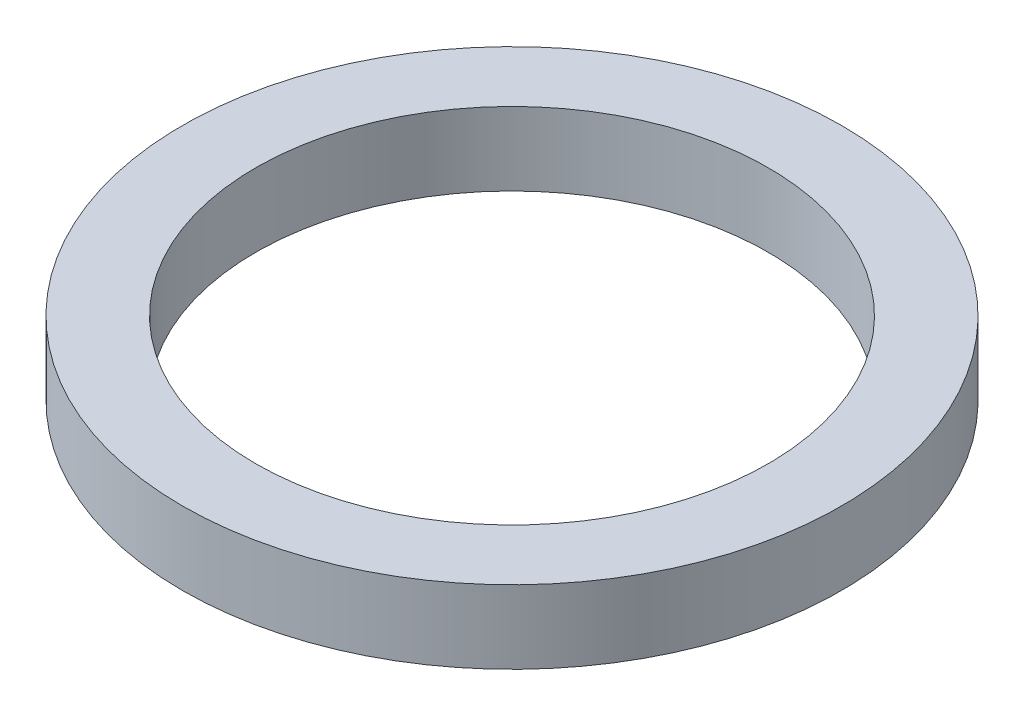
SolidWorks part; units mm, degrees
material "1060 Alloy"
ref_plane "Front Plane" through (0, 0, 0) normal (0, 0, 1) x (1, 0, 0)
ref_plane "Top Plane" through (0, 0, 0) normal (0, 1, 0) x (1, 0, 0)
ref_plane "Right Plane" through (0, 0, 0) normal (1, 0, 0) x (0, 0, -1)
sketch "Sketch1" plane through (0, 0, 0) normal (0, 1, 0) x (1, 0, 0)
  circle A0 centre (0, 0) radius 45
  circle A1 centre (0, 0) radius 35
  dimension "D1" = 90
  dimension "D2" = 70
extrude "Boss-Extrude1" add sketch "Sketch1" along normal blind 10
